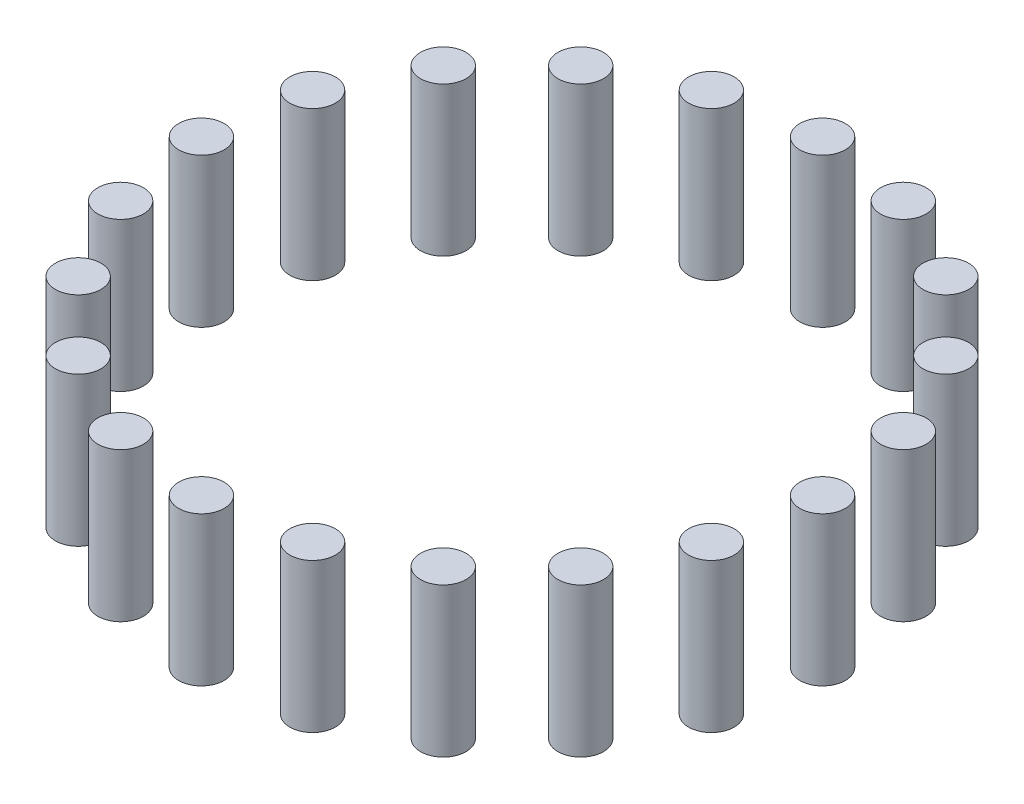
SolidWorks part; units mm, degrees
ref_plane "Front Plane" through (0, 0, 0) normal (0, 0, 1) x (1, 0, 0)
ref_plane "Top Plane" through (0, 0, 0) normal (0, 1, 0) x (1, 0, 0)
ref_plane "Right Plane" through (0, 0, 0) normal (1, 0, 0) x (0, 0, -1)
sketch "Sketch1" plane through (0, 0, 0) normal (0, 1, 0) x (1, 0, 0)
  circle A0 centre (0, 0) radius 75
  circle A1 centre (75, 0) radius 5.5
  circle A2 centre (71.3292, -23.1763) radius 5.5
  circle A3 centre (60.6763, -44.0839) radius 5.5
  circle A4 centre (44.0839, -60.6763) radius 5.5
  circle A5 centre (23.1763, -71.3292) radius 5.5
  circle A6 centre (0, -75) radius 5.5
  circle A7 centre (-23.1763, -71.3292) radius 5.5
  circle A8 centre (-44.0839, -60.6763) radius 5.5
  circle A9 centre (-60.6763, -44.0839) radius 5.5
  circle A10 centre (-71.3292, -23.1763) radius 5.5
  circle A11 centre (-75, 0) radius 5.5
  circle A12 centre (-71.3292, 23.1763) radius 5.5
  circle A13 centre (-60.6763, 44.0839) radius 5.5
  circle A14 centre (-44.0839, 60.6763) radius 5.5
  circle A15 centre (-23.1763, 71.3292) radius 5.5
  circle A16 centre (0, 75) radius 5.5
  circle A17 centre (23.1763, 71.3292) radius 5.5
  circle A18 centre (44.0839, 60.6763) radius 5.5
  circle A19 centre (60.6763, 44.0839) radius 5.5
  circle A20 centre (71.3292, 23.1763) radius 5.5
  point P48 (0, 0)
  dimension "D1" = 20
extrude "Boss-Extrude1" add sketch "Sketch1" along normal blind 36 contours A0 A15 | A0 A15
